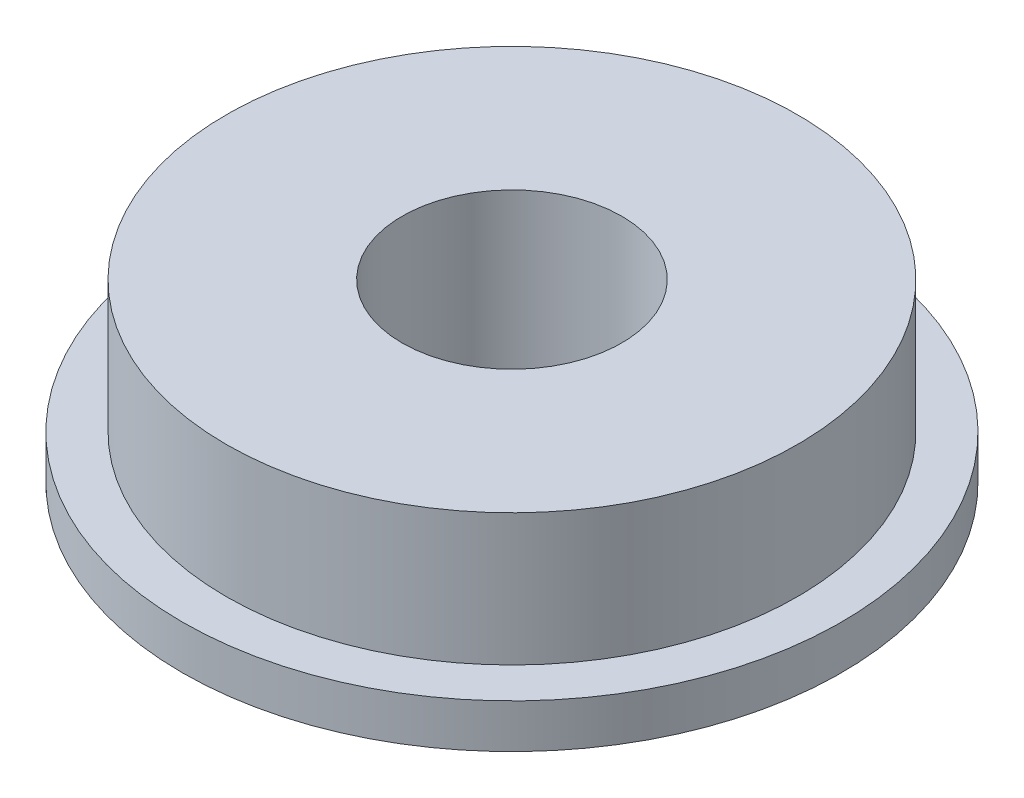
SolidWorks part; units mm, degrees
ref_plane "前视基准面" through (0, 0, 0) normal (0, 0, 1) x (1, 0, 0)
ref_plane "上视基准面" through (0, 0, 0) normal (0, 1, 0) x (1, 0, 0)
ref_plane "右视基准面" through (0, 0, 0) normal (1, 0, 0) x (0, 0, -1)
sketch "草图1" plane through (0, 0, 0) normal (0, 0, 1) x (1, 0, 0)
  line L0 (2.5, 0) -> (7.5, 0)
  line L1 (7.5, 0) -> (7.5, 1)
  line L2 (7.5, 1) -> (6.5, 1)
  line L3 (6.5, 1) -> (6.5, 4)
  line L4 (6.5, 4) -> (2.5, 4)
  line L5 (0, 4) -> (0, 0) construction
  line L6 (2.5, 4) -> (2.5, 0)
  point P9 (0, 0)
  point P10 (0, 0)
revolve "旋转1" add sketch "草图1" angle 360 about L5
